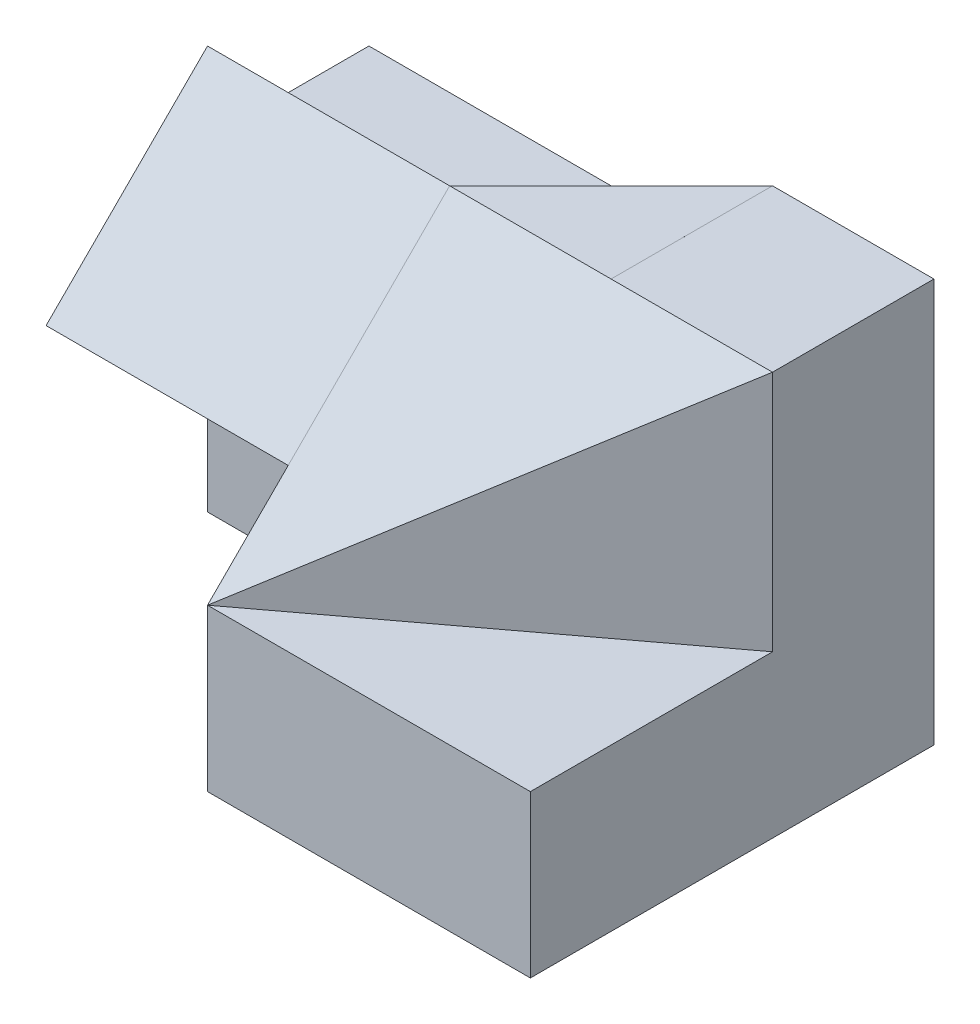
SolidWorks part; units mm, degrees
ref_plane "Front Plane" through (0, 0, 0) normal (0, 0, 1) x (1, 0, 0)
ref_plane "Top Plane" through (0, 0, 0) normal (0, 1, 0) x (1, 0, 0)
ref_plane "Right Plane" through (0, 0, 0) normal (1, 0, 0) x (0, 0, -1)
sketch "Sketch1" plane through (0, 0, 0) normal (0, 0, 1) x (1, 0, 0)
  line L1 (0, 0) -> (70, 0)
  line L2 (0, 0) -> (0, 50)
  line L3 (0, 50) -> (70, 50)
  line L4 (70, 0) -> (70, 50)
  dimension "D1" = 70
  dimension "D2" = 50
extrude "Boss-Extrude1" add sketch "Sketch1" along normal blind 50
sketch "Sketch2" plane through (0, 50, 0) normal (0, 1, 0) x (1, 0, 0)
  line L1 (0, -50) -> (30, -50)
  line L2 (0, -50) -> (0, -40)
  line L3 (0, -40) -> (30, -40)
  line L4 (30, -50) -> (30, -40)
  dimension "D1" = 30
  dimension "D2" = 10
extrude "Cut-Extrude1" cut sketch "Sketch2" against normal blind 50
sketch "Sketch3" plane through (0, 0, 0) normal (-1, 0, 0) x (0, 0, 1)
  line L0 (0, 50) -> (20, 50)
  line L1 (40, 50) -> (0, 50) construction
  line L2 (20, 50) -> (50, 20)
  line L3 (50, 20) -> (50, 0)
  line L4 (50, 0) -> (0, 0)
  line L5 (20, 50) -> (50, 50)
  line L6 (50, 20) -> (50, 50)
  line M2 (40, 0) -> (40, 50)
  line M3 (40, 50) -> (0, 50)
  dimension "D1" = 20
  dimension "D2" = 30
  dimension "D3" = 30
extrude "Cut-Extrude2" cut sketch "Sketch3" against normal blind 91 contours L2 M3 M2 | L2 L6 L5 M2
sketch "Sketch6" plane through (0, 0, 0) normal (-1, 0, 0) x (0, 0, 1)
  line L0 (40, 30) -> (20, 30)
  line L1 (20, 30) -> (20, 0)
  line L2 (40, 0) -> (0, 0) construction
  line L3 (20, 0) -> (40, 0)
  line L4 (40, 0) -> (40, 30)
  dimension "D1" = 20
extrude "Cut-Extrude7" cut sketch "Sketch6" against normal blind 30
ref_plane "Plane2" through (0, 0, 50) normal (0, 0, 1) x (1, 0, 0)
sketch "Sketch10" plane through (0, 0, 50) normal (0, 0, 1) x (1, 0, 0)
  line L0 (30, 20) -> (70, 20)
  line L1 (70, 20) -> (70, 50)
  line L2 (70, 50) -> (50, 50)
  line L3 (50, 50) -> (30, 30)
  line L4 (30, 30) -> (30, 20)
  dimension "D1" = 10
  dimension "D2" = 30
  dimension "D3" = 20
extrude "Cut-Extrude11" cut sketch "Sketch10" against normal blind 30
ref_plane "Plane3" through (0, 50, 0) normal (0, 1, 0) x (1, 0, 0)
sketch "Sketch11" plane through (0, 50, 0) normal (0, 1, 0) x (1, 0, 0)
  line L0 (30, -20) -> (50, 0)
  line L1 (50, -20) -> (0, -20) construction
  line L2 (70, 0) -> (0, 0) construction
  line L3 (50, 0) -> (50, -20)
  line L4 (50, -20) -> (30, -50)
  line L5 (30, -50) -> (30, -20)
  line L6 (50, 0) -> (0, 0)
  line L7 (0, 0) -> (0, -20)
  line L8 (0, -20) -> (30, -20)
  dimension "D1" = 20
  dimension "D2" = 30
  dimension "D3" = 40
extrude "Cut-Extrude12" cut sketch "Sketch11" against normal blind 10 contours L7 L8 L0 L6
sketch "Sketch12" plane through (30, 0, 0) normal (-1, 0, 0) x (0, 0, 1)
  line L0 (20, 20) -> (20, 29.999)
  line L1 (20, 29.999) -> (40.001, 29.999)
  line L2 (40.001, 29.999) -> (50, 20)
  line L3 (50, 20) -> (20.001, 20)
  line L4 (20, 20) -> (50, 20) construction
  line L9 (50, 0) -> (50, 20)
  line L10 (50, 20) -> (20, 20)
  line L11 (20, 20) -> (20, 0)
  line L12 (20, 0) -> (50, 0)
  line L13 (50, 0) -> (50, 20)
  line L14 (50, 20) -> (20.001, 20)
  line L15 (20, 20) -> (20, 0)
  line L16 (20, 0) -> (50, 0)
  dimension "D1" = 29.999
  dimension "D2" = 9.999
  dimension "D3" = 9.999
  dimension "D4" = 0
extrude "Boss-Extrude8" add sketch "Sketch12" against normal blind 10 contours L2 L1 L0 L14
sketch "Sketch17" plane through (0, 50, 0) normal (0, 1, 0) x (1, 0, 0)
  line L1 (70, 0) -> (50, 0)
  line L2 (70, 0) -> (70, -20)
  line L3 (70, -20) -> (50, -20)
  line L4 (50, 0) -> (50, -20)
extrude "Cut-Extrude14" cut sketch "Sketch17" against normal blind 0.0001
sketch "Sketch18" plane through (0, 50, 0) normal (0, 1, 0) x (1, 0, 0)
  line L0 (50, 0) -> (30, -20)
  line L1 (30, -20) -> (50, 0) construction
  line L2 (30, -20) -> (30, -50)
  line L3 (30, -50) -> (50, -20)
  line L4 (50, -20) -> (50, 0)
  dimension "D1" = 30
extrude "Boss-Extrude19" add sketch "Sketch18" against normal blind 30
ref_plane "Plane4" through (34.8, 0, 46.4) normal (-0.6, 0, -0.8) x (-0.8, 0, 0.6)
sketch "Sketch19" plane through (34.8, 0, 46.4) normal (-0.6, 0, -0.8) x (-0.8, 0, 0.6)
  line L1 (6, 20) -> (-44, 20)
  line L2 (-44, 20) -> (-44, 49.9999)
  line L3 (-44, 49.9999) -> (6, 50)
  line L4 (6, 50) -> (6, 20)
extrude "Boss-Extrude20" add sketch "Sketch19" along normal blind 20
sketch "Sketch21" plane through (34.8, 0, 46.4) normal (0.6, 0, 0.8) x (0.8, 0, -0.6)
  line L0 (6.5, 27.5) -> (6.5, 20)
  line L1 (6.5, 20) -> (-6, 20)
  line L2 (-6, 20) -> (6.5, 27.5)
extrude "Cut-Extrude15" cut sketch "Sketch21" along normal blind 20
sketch "Sketch22" plane through (0.0001, 50, -0.0001) normal (0, 1, 0) x (1, 0, 0)
  line L0 (29.9999, -25.0001) -> (29.9999, -50.0001)
  line L1 (29.9999, -50.0001) -> (17.9999, -34.0001)
  line L2 (17.9999, -34.0001) -> (29.9999, -25.0001)
extrude "Cut-Extrude16" cut sketch "Sketch22" against normal blind 54
sketch "Sketch23" plane through (29.9999, 0, 0) normal (-1, 0, 0) x (0, 0, 1)
  line L0 (20, 50) -> (50, 20)
  line L1 (25, 45) -> (20, 50) construction
  line L2 (20, 50) -> (50, 50) construction
  line L3 (50, 20) -> (50, 50)
  line L4 (50, 50) -> (20, 50)
extrude "Cut-Extrude17" cut sketch "Sketch23" against normal blind 54
sketch "Sketch27" plane through (0, 0, 0) normal (-1, 0, 0) x (0, 0, 1)
  line L0 (20, 50) -> (20, 30)
  line L1 (20, 30) -> (40, 30)
  line L2 (40, 30) -> (20, 50)
extrude "Boss-Extrude28" add sketch "Sketch27" against normal blind 30
sketch "Sketch28" plane through (0, 0, 0) normal (-1, 0, 0) x (0, 0, 1)
  line L1 (20, 30) -> (50, 30)
  line L2 (20, 30) -> (20, 0)
  line L3 (20, 0) -> (50, 0)
  line L4 (50, 30) -> (50, 0)
  dimension "D1" = 30
  dimension "D2" = 30
extrude "Boss-Extrude30" add sketch "Sketch28" against normal blind 31
sketch "Sketch29" plane through (0, 0, 0) normal (-1, 0, 0) x (0, 0, 1)
  line L1 (50, 0) -> (20, 0)
  line L2 (50, 0) -> (50, 30)
  line L3 (50, 30) -> (20, 30)
  line L4 (20, 0) -> (20, 30)
  dimension "D1" = 30
  dimension "D2" = 30
extrude "Cut-Extrude20" cut sketch "Sketch29" against normal blind 30
sketch "Sketch30" plane through (31, 0, 0) normal (1, 0, 0) x (0, 0, -1)
  line L0 (-40, 30) -> (-50, 20)
  line L1 (-50, 20) -> (-50, 30)
  line L2 (-50, 30) -> (-40, 30)
extrude "Cut-Extrude21" cut sketch "Sketch30" against normal blind 30
sketch "Sketch31" plane through (0, 20, 0) normal (0, 1, 0) x (1, 0, 0)
  line L0 (31, -49.25) -> (30, -50)
  line L1 (30, -50) -> (31, -50)
  line L2 (31, -50) -> (31, -49.25)
extrude "Cut-Extrude22" cut sketch "Sketch31" along normal blind 30
sketch "Sketch32" plane through (0.0001, 50, 0) normal (0, -1, 0) x (1, 0, 0)
  line L1 (49.9999, 20) -> (69.9999, 20)
  line L2 (49.9999, 20) -> (49.9999, 0)
  line L3 (49.9999, 0) -> (69.9999, 0)
  line L4 (69.9999, 20) -> (69.9999, 0)
extrude "Cut-Extrude23" cut sketch "Sketch32" along normal blind 0.0001
sketch "Sketch33" plane through (0, 50, 0) normal (0, 1, 0) x (1, 0, 0)
  line L0 (30, -50) -> (30, -20)
  line L1 (30, -20) -> (50, -20)
  line L2 (50, -20) -> (30, -50)
extrude "Cut-Extrude39" cut sketch "Sketch33" against normal blind 0.0001
ref_plane "Plane7" through (70, 20, 20) normal (-0.8, 0, 0.6) x (0.6, 0, 0.8)
